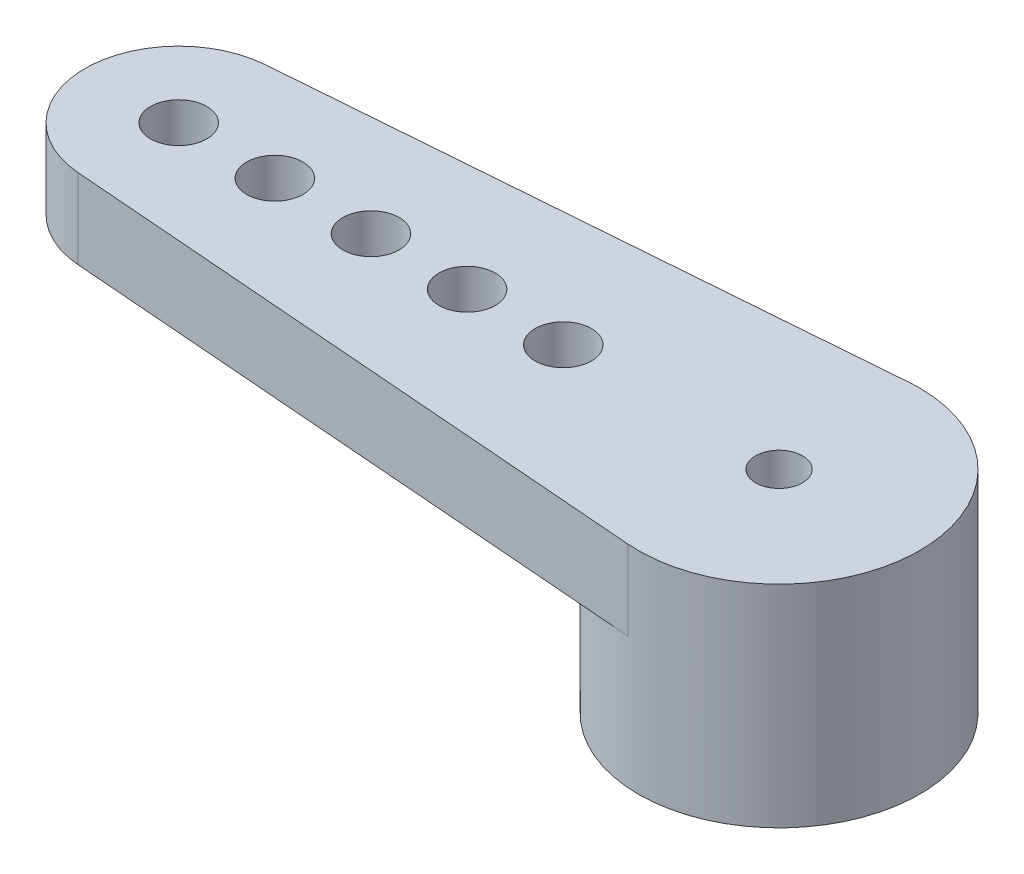
SolidWorks part; units mm, degrees
ref_plane "Front Plane" through (0, 0, 0) normal (0, 0, 1) x (1, 0, 0)
ref_plane "Top Plane" through (0, 0, 0) normal (0, 1, 0) x (1, 0, 0)
ref_plane "Right Plane" through (0, 0, 0) normal (1, 0, 0) x (0, 0, -1)
sketch "Sketch1" plane through (0, 0, 0) normal (0, 1, 0) x (1, 0, 0)
  line L0 (-14.8, 0) -> (3, 0)
  line L1 (-12.9563, 1.9939) -> (-0.2344, 2.9908)
  line L2 (-12.9563, -1.9939) -> (-0.2344, -2.9908)
  circle A0 centre (0, 0) radius 3
  circle A1 centre (-12.8, 0) radius 2
  dimension "D1" = 6
  dimension "D2" = 4
  dimension "D3" = 17.8
extrude "Boss-Extrude1" add sketch "Sketch1" along normal blind 1.7 contours A1 L2 A0 L0 | L0 A1 | L0 A1 | A1 L0 A0 L1 | L0 A0 | L0 A0
sketch "Sketch2" plane through (0, 1.7, 0) normal (0, 1, 0) x (1, 0, 0)
  circle A0 centre (-12.8, 0) radius 0.6
  circle A1 centre (-10.75, 0) radius 0.6
  circle A2 centre (-8.7, 0) radius 0.6
  circle A3 centre (-6.65, 0) radius 0.6
  circle A4 centre (-4.6, 0) radius 0.6
  arc A5 (-12.9562, 1.9939) -> (-12.9562, -1.9939) centre (-12.8, 0) ccw construction
  point P13 (-14.8, 0)
  point P14 (-11.0819, -1.1034)
  point P15 (0, 0)
  dimension "D1" = 1.2
  dimension "D3" = 2
  dimension "D4" = 2.05
  dimension "D2" = 5
extrude "Cut-Extrude1" cut sketch "Sketch2" against normal through all
sketch "Sketch3" plane through (0, 0, 0) normal (0, -1, 0) x (1, 0, 0)
  circle A0 centre (0, 0) radius 3
  dimension "D1" = 6
extrude "Boss-Extrude2" add sketch "Sketch3" along normal blind 2.8
sketch "Sketch4" plane through (0, -2.8, 0) normal (0, -1, 0) x (1, 0, 0)
  circle A0 centre (0, 0) radius 0.5
  dimension "D1" = 1
extrude "Cut-Extrude2" cut sketch "Sketch4" against normal through all
